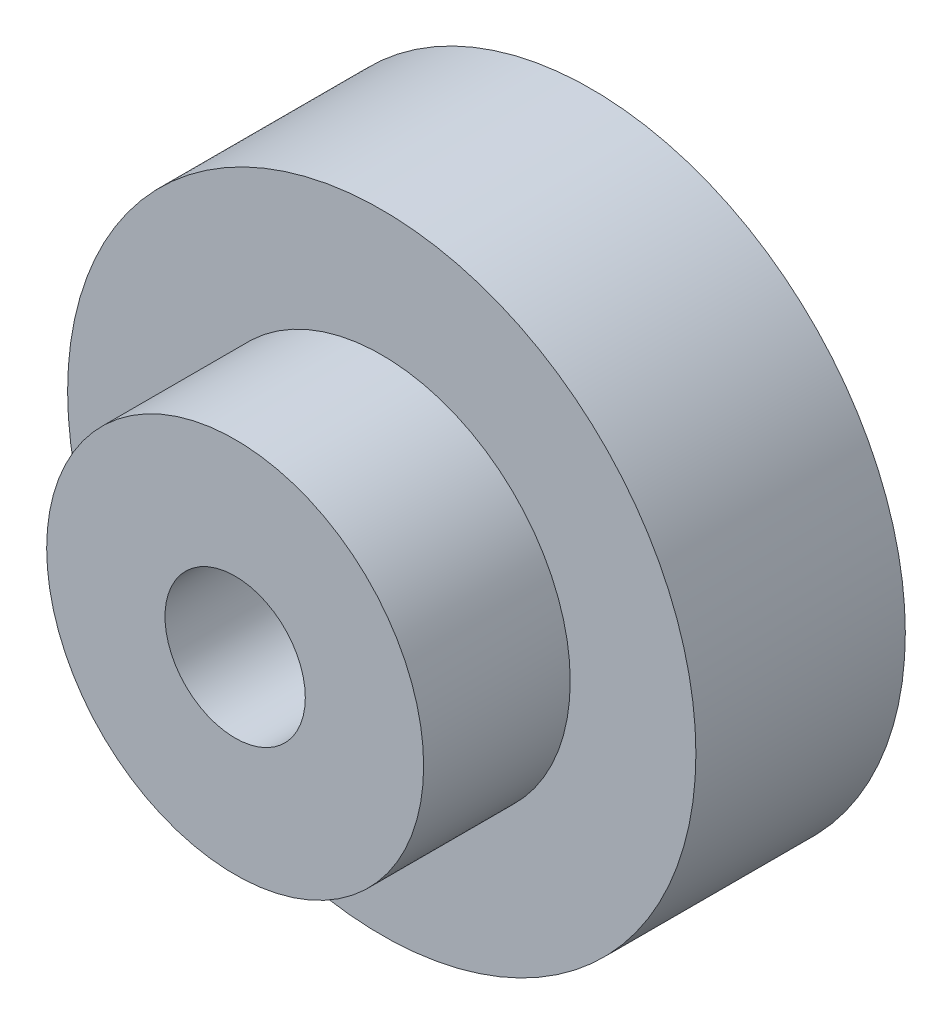
SolidWorks part; units mm, degrees
ref_plane "Plano frontal" through (0, 0, 0) normal (0, 0, 1) x (1, 0, 0)
ref_plane "Plano superior" through (0, 0, 0) normal (0, 1, 0) x (1, 0, 0)
ref_plane "Plano direito" through (0, 0, 0) normal (1, 0, 0) x (0, 0, -1)
sketch "Esboço1" plane through (0, 0, 0) normal (0, 0, 1) x (1, 0, 0)
  circle A0 centre (0, 0) radius 3.35
  circle A1 centre (0, 0) radius 15
extrude "Ressalto-extrusão1" add sketch "Esboço1" along normal blind 10
sketch "Esboço2" plane through (0, 0, 10) normal (0, 0, 1) x (1, 0, 0)
  circle A0 centre (0, 0) radius 9
  circle A1 centre (0, 0) radius 3.35 construction
  circle A2 centre (0, 0) radius 3.35
extrude "Ressalto-extrusão2" add sketch "Esboço2" along normal blind 7
